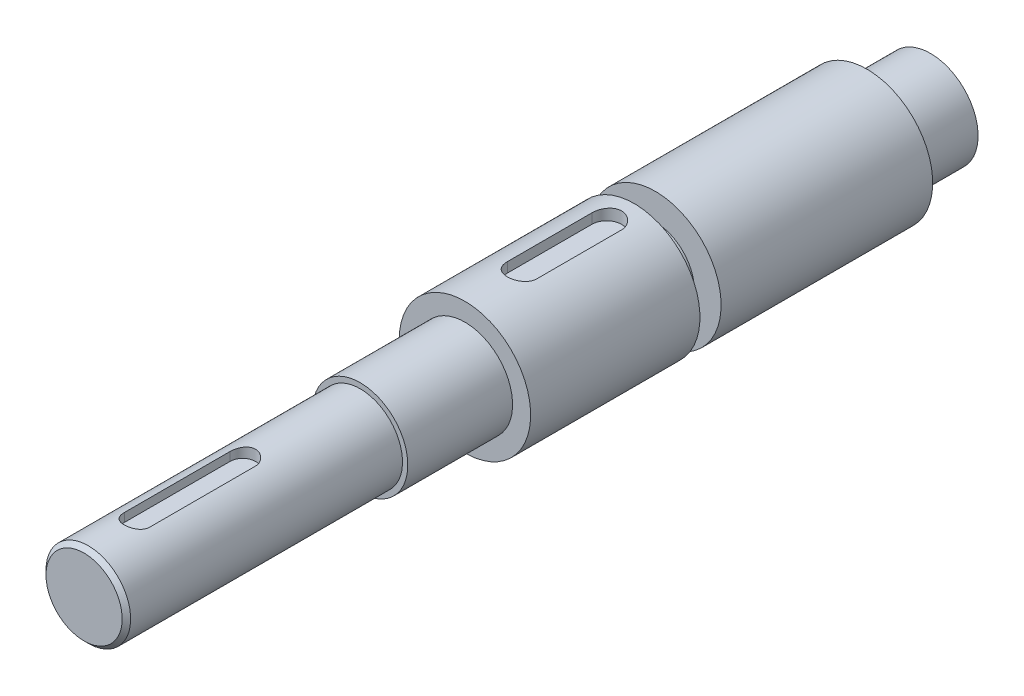
SolidWorks part; units mm, degrees
material "AISI 1020"
ref_plane "Front Plane" through (0, 0, 0) normal (0, 0, 1) x (1, 0, 0)
ref_plane "Top Plane" through (0, 0, 0) normal (0, 1, 0) x (1, 0, 0)
ref_plane "Right Plane" through (0, 0, 0) normal (1, 0, 0) x (0, 0, -1)
sketch "Sketch1" plane through (0, 0, 0) normal (0, 1, 0) x (1, 0, 0)
  line L0 (0, 0) -> (0, -400)
  line L3 (22.5, -30) -> (31.0462, -30)
  line L4 (31.0462, -30) -> (31.0462, -130)
  line L5 (31.0462, -130) -> (18.4131, -130)
  line L7 (31.0462, -220) -> (22.5, -220)
  line L8 (22.5, -220) -> (22.5, -269.5144)
  line L9 (22.5, -269.5144) -> (20, -269.5144)
  line L10 (20, -269.5144) -> (20, -400)
  line L11 (20, -400) -> (0, -400)
  line L12 (22.5, -30) -> (22.5, 0)
  line L13 (22.5, 0) -> (0, 0)
  line L14 (18.4131, -130) -> (18.4131, -140)
  line L15 (18.4131, -140) -> (31.0462, -140)
  line L16 (31.0462, -140) -> (31.0462, -220)
  dimension "D2" = 400
  dimension "D7" = 20
revolve "Revolve1" add sketch "Sketch1" angle 360 about L0
sketch "Sketch2" plane through (-0.9582, 7.9831, 400) normal (0, 0, 1) x (1, 0, 0)
  line L0 (0.9582, 12.0169) -> (0.9582, -7.9831) construction
  line L1 (0.9582, -7.9831) -> (0.9582, 12.0169) construction
  circle A0 centre (0.9582, -7.9831) radius 20 construction
  circle A2 centre (0.9582, -7.9831) radius 20
  dimension "Angle from vertical" = 360
ref_plane "Plane1" through (0, 20, 400) normal (0, -1, 0) x (-1, 0, 0)
sketch "Sketch3" plane through (0, 20, 400) normal (0, -1, 0) x (0, 0, 1)
  line L0 (-25, 0) -> (-75, 0) construction
  line L1 (-25, 6) -> (-75, 6)
  line L2 (-25, -6) -> (-75, -6)
  arc A0 (-25, 6) -> (-25, -6) centre (-25, 0) cw
  arc A1 (-75, 6) -> (-75, -6) centre (-75, 0) ccw
  dimension "Keyway width" = 12
  dimension "Distance from end face" = 25
  dimension "Length of slot" = 50
extrude "Cut-Extrude1" cut sketch "Sketch3" along normal blind 5
other "keyway (bs 4235 - part i)<1>"
sketch "Sketch22" plane through (8.0669, 22.5362, 220) normal (0, 0, 1) x (1, 0, 0)
  line L0 (-8.0669, 8.51) -> (-8.0669, -22.5362) construction
  line L1 (-8.0669, -22.5362) -> (-8.0669, 8.51) construction
  circle A0 centre (-8.0669, -22.5362) radius 31.0462 construction
  circle A2 centre (-8.0669, -22.5362) radius 31.0462
  dimension "Angle from vertical" = 0
ref_plane "Plane12" through (0, 31.0462, 220) normal (0, -1, 0) x (-1, 0, 0)
sketch "Sketch32" plane through (0, 31.0462, 220) normal (0, -1, 0) x (0, 0, 1)
  line L0 (-27, 0) -> (-67, 0) construction
  line L1 (-27, 7) -> (-67, 7)
  line L2 (-27, -7) -> (-67, -7)
  arc A0 (-27, 7) -> (-27, -7) centre (-27, 0) cw
  arc A1 (-67, 7) -> (-67, -7) centre (-67, 0) ccw
  dimension "Keyway width" = 14
  dimension "Distance from end face" = 27
  dimension "Length of slot" = 40
extrude "Cut-Extrude12" cut sketch "Sketch32" along normal blind 5.5
other "keyway (bs 4235 - part i)<2>"
chamfer "Chamfer1" distance 2 angle 45 1 edges at (-20, 0, 400)
